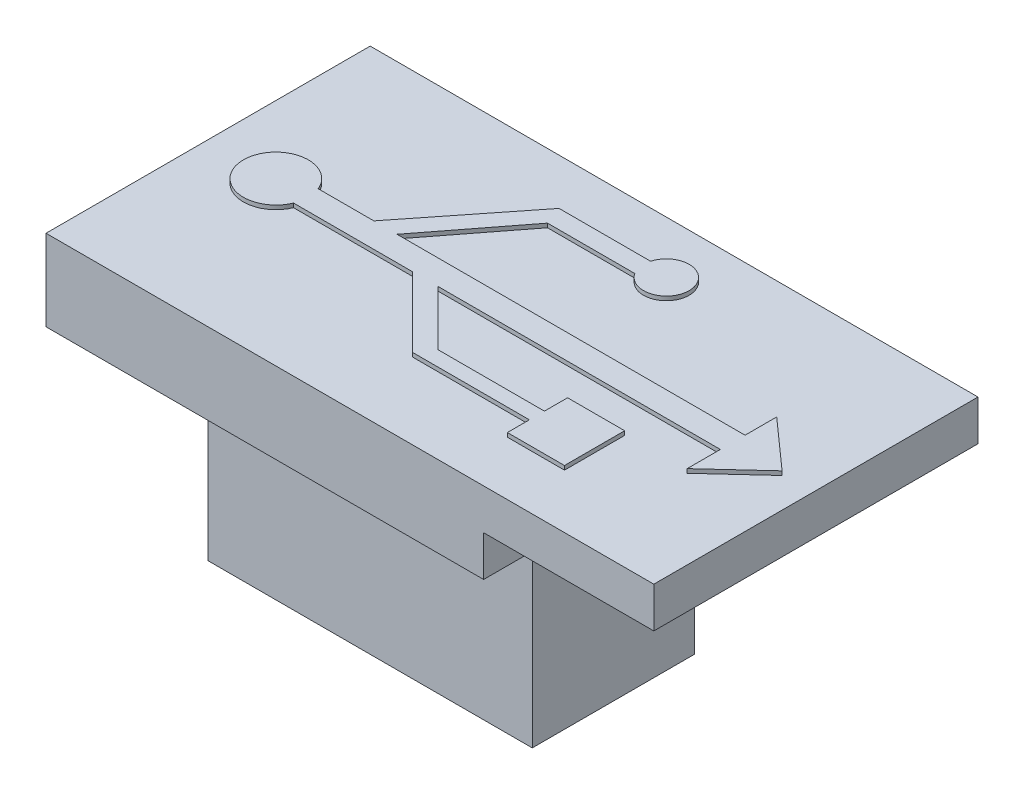
SolidWorks part; units mm, degrees
ref_plane "Plan de face" through (0, 0, 0) normal (0, 0, 1) x (1, 0, 0)
ref_plane "Plan de dessus" through (0, 0, 0) normal (0, 1, 0) x (1, 0, 0)
ref_plane "Plan de droite" through (0, 0, 0) normal (1, 0, 0) x (0, 0, -1)
sketch "Esquisse2" plane through (0, 0, 0) normal (0, 1, 0) x (1, 0, 0)
  line L1 (0, 0) -> (15, 0)
  line L2 (0, 0) -> (0, 8)
  line L3 (0, 8) -> (15, 8)
  line L4 (15, 0) -> (15, 8)
  dimension "D1" = 15
  dimension "D2" = 8
extrude "Extrusion1" add sketch "Esquisse2" along normal blind 1
sketch "Esquisse3" plane through (0, 0, 0) normal (0, -1, 0) x (1, 0, 0)
  line L0 (15, -8) -> (0, -8) construction
  line L1 (0, 0) -> (10.8, 0)
  line L2 (0, 0) -> (0, -8)
  line L3 (0, -8) -> (10.8, -8)
  line L4 (10.8, 0) -> (10.8, -8)
  dimension "D1" = 10.8
extrude "Extrusion2" add sketch "Esquisse3" along normal blind 1
sketch "Esquisse4" plane through (0, -1, 0) normal (0, -1, 0) x (1, 0, 0)
  line L0 (0, 0) -> (0, -8) construction
  line L1 (2, -2) -> (10, -2)
  line L2 (2, -2) -> (2, -6)
  line L3 (2, -6) -> (10, -6)
  line L4 (10, -2) -> (10, -6)
  line L5 (10.8, 0) -> (0, 0) construction
  dimension "D1" = 8
  dimension "D2" = 4
  dimension "D3" = 2
  dimension "D4" = 2
extrude "Extrusion3" add sketch "Esquisse4" along normal blind 5
sketch "Esquisse5" plane through (0, -6, 0) normal (0, -1, 0) x (1, 0, 0)
  line L0 (10, -2) -> (2, -2) construction
  line L1 (2.5484, -2.3) -> (3.0245, -2.3)
  line L2 (2.5484, -2.3) -> (2.5484, -3.1)
  line L3 (2.5484, -3.1) -> (3.0245, -3.1)
  line L4 (3.0245, -2.3) -> (3.0245, -3.1)
  line L5 (4.6484, -2.3) -> (5.1245, -2.3)
  line L6 (4.6484, -2.3) -> (4.6484, -3.1)
  line L7 (4.6484, -3.1) -> (5.1245, -3.1)
  line L8 (5.1245, -2.3) -> (5.1245, -3.1)
  line L9 (6.7484, -2.3) -> (7.2245, -2.3)
  line L10 (6.7484, -2.3) -> (6.7484, -3.1)
  line L11 (6.7484, -3.1) -> (7.2245, -3.1)
  line L12 (7.2245, -2.3) -> (7.2245, -3.1)
  line L13 (8.8484, -2.3) -> (9.3245, -2.3)
  line L14 (8.8484, -2.3) -> (8.8484, -3.1)
  line L15 (8.8484, -3.1) -> (9.3245, -3.1)
  line L16 (9.3245, -2.3) -> (9.3245, -3.1)
  line L17 (2.5484, -4.8) -> (3.0245, -4.8)
  line L18 (2.5484, -4.8) -> (2.5484, -5.6)
  line L19 (2.5484, -5.6) -> (3.0245, -5.6)
  line L20 (3.0245, -4.8) -> (3.0245, -5.6)
  line L21 (4.6484, -4.8) -> (5.1245, -4.8)
  line L22 (4.6484, -4.8) -> (4.6484, -5.6)
  line L23 (4.6484, -5.6) -> (5.1245, -5.6)
  line L24 (5.1245, -4.8) -> (5.1245, -5.6)
  line L25 (6.7484, -4.8) -> (7.2245, -4.8)
  line L26 (6.7484, -4.8) -> (6.7484, -5.6)
  line L27 (6.7484, -5.6) -> (7.2245, -5.6)
  line L28 (7.2245, -4.8) -> (7.2245, -5.6)
  line L29 (8.8484, -4.8) -> (9.3245, -4.8)
  line L30 (8.8484, -4.8) -> (8.8484, -5.6)
  line L31 (8.8484, -5.6) -> (9.3245, -5.6)
  line L32 (9.3245, -4.8) -> (9.3245, -5.6)
  dimension "D1" = 0.3
  dimension "D2" = 0.8
extrude "Extrusion4" cut sketch "Esquisse5" against normal blind 3
sketch "Esquisse6" plane through (0, 1, 0) normal (0, 1, 0) x (1, 0, 0)
  line L0 (13.042, 4.2095) -> (13.042, 4.9903)
  line L1 (10.052, 2.8192) -> (11.4613, 2.8192)
  line L2 (10.052, 2.8192) -> (10.052, 2.2479)
  line L3 (10.052, 1.3338) -> (11.4613, 1.3338)
  line L4 (11.4613, 2.8192) -> (11.4613, 1.3338)
  line L5 (2.5084, 4.2095) -> (3.8815, 4.2095)
  line L6 (3.8815, 4.2095) -> (5.9003, 6.7615)
  line L7 (2.5084, 3.6001) -> (5.4432, 3.6001)
  line L8 (5.9003, 6.7615) -> (8.1581, 6.7615)
  line L9 (13.042, 4.9903) -> (14.2608, 3.9048)
  line L10 (14.2608, 3.9048) -> (13.042, 2.7811)
  line L11 (13.042, 2.7811) -> (13.042, 3.6001)
  line L12 (4.4529, 4.2095) -> (6.0717, 6.3044)
  line L13 (6.0717, 6.3044) -> (8.2268, 6.3044)
  line L14 (4.4529, 4.2095) -> (13.042, 4.2095)
  line L15 (5.4432, 3.6001) -> (7.1667, 1.8765)
  line L16 (7.1667, 1.8765) -> (10.052, 1.8765)
  line L17 (6.0717, 3.6001) -> (7.4238, 2.2479)
  line L18 (7.4238, 2.2479) -> (10.052, 2.2479)
  line L19 (6.0717, 3.6001) -> (13.042, 3.6001)
  line L20 (10.052, 1.8765) -> (10.052, 1.3338)
  arc A0 (2.5084, 4.2095) -> (2.5084, 3.6001) centre (1.7676, 3.9048) ccw
  arc A1 (8.2268, 6.3044) -> (8.1581, 6.7615) centre (8.6998, 6.6091) ccw
extrude "Extrusion5" add sketch "Esquisse6" along normal blind 0.1
